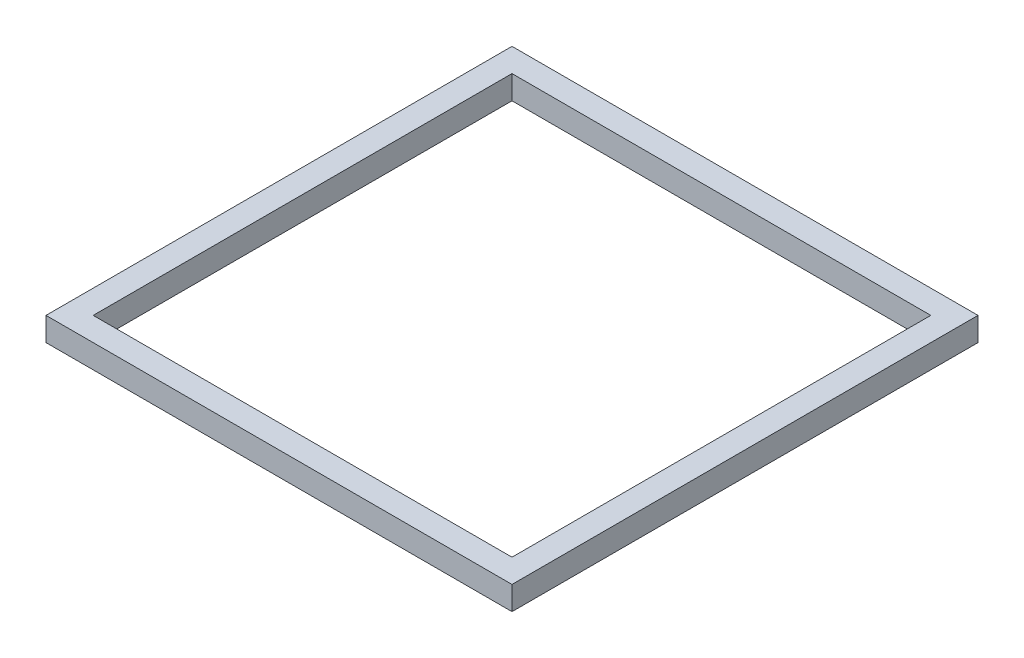
SolidWorks part; units mm, degrees
material "Acrylic (Medium-high impact)"
ref_plane "Front Plane" through (0, 0, 0) normal (0, 0, 1) x (1, 0, 0)
ref_plane "Top Plane" through (0, 0, 0) normal (0, 1, 0) x (1, 0, 0)
ref_plane "Right Plane" through (0, 0, 0) normal (1, 0, 0) x (0, 0, -1)
sketch "Sketch1" plane through (0, 0, 0) normal (0, 1, 0) x (1, 0, 0)
  line L1 (-62.7, -62.7) -> (62.7, -62.7)
  line L2 (-62.7, -62.7) -> (-62.7, 62.7)
  line L3 (-62.7, 62.7) -> (62.7, 62.7)
  line L4 (62.7, -62.7) -> (62.7, 62.7)
  line L5 (-62.7, -62.7) -> (62.7, 62.7) construction
  line L6 (-62.7, 62.7) -> (62.7, -62.7) construction
  point P0 (0, 0)
  dimension "D1" = 125.4
  dimension "D2" = 125.4
extrude "Boss-Extrude1" add sketch "Sketch1" along normal blind 6.35
sketch "Sketch2" plane through (0, 6.35, 0) normal (0, 1, 0) x (1, 0, 0)
  line L1 (-56.35, -56.35) -> (56.35, -56.35)
  line L2 (-56.35, -56.35) -> (-56.35, 56.35)
  line L3 (-56.35, 56.35) -> (56.35, 56.35)
  line L4 (56.35, -56.35) -> (56.35, 56.35)
  line L5 (-56.35, -56.35) -> (56.35, 56.35) construction
  line L6 (-56.35, 56.35) -> (56.35, -56.35) construction
  point P0 (0, 0)
  dimension "D1" = 112.7
  dimension "D2" = 112.7
extrude "Cut-Extrude1" cut sketch "Sketch2" against normal through all
